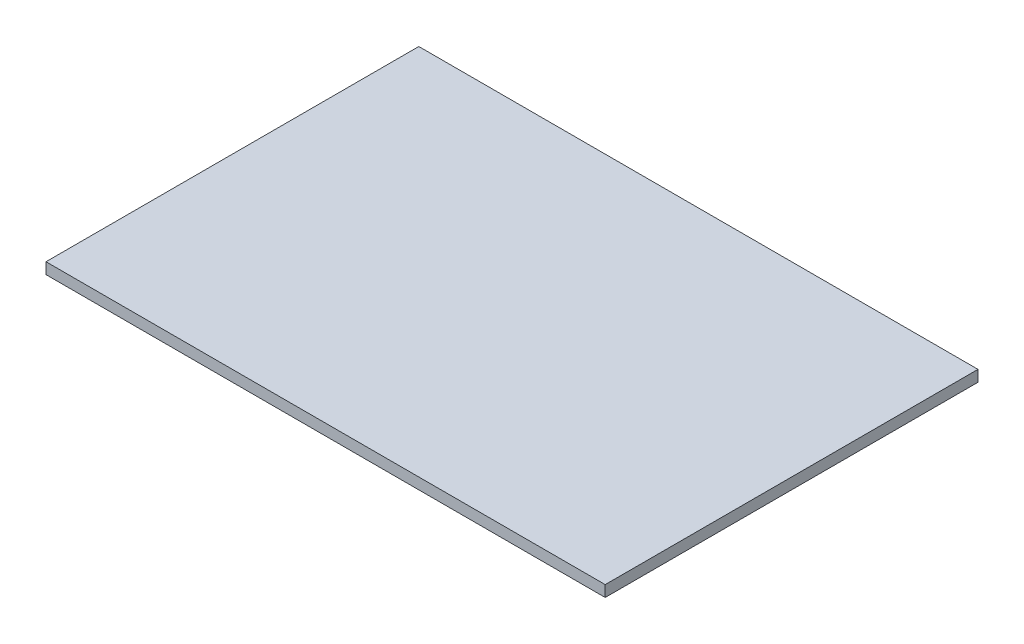
SolidWorks part; units mm, degrees
ref_plane "Front Plane" through (0, 0, 0) normal (0, 0, 1) x (1, 0, 0)
ref_plane "Top Plane" through (0, 0, 0) normal (0, 1, 0) x (1, 0, 0)
ref_plane "Right Plane" through (0, 0, 0) normal (1, 0, 0) x (0, 0, -1)
sketch "Sketch1" plane through (0, 0, 0) normal (0, 1, 0) x (1, 0, 0)
  line L1 (0, 0) -> (150, 0)
  line L2 (0, 0) -> (0, 100)
  line L3 (0, 100) -> (150, 100)
  line L4 (150, 0) -> (150, 100)
extrude "Boss-Extrude1" add sketch "Sketch1" along normal blind 3
